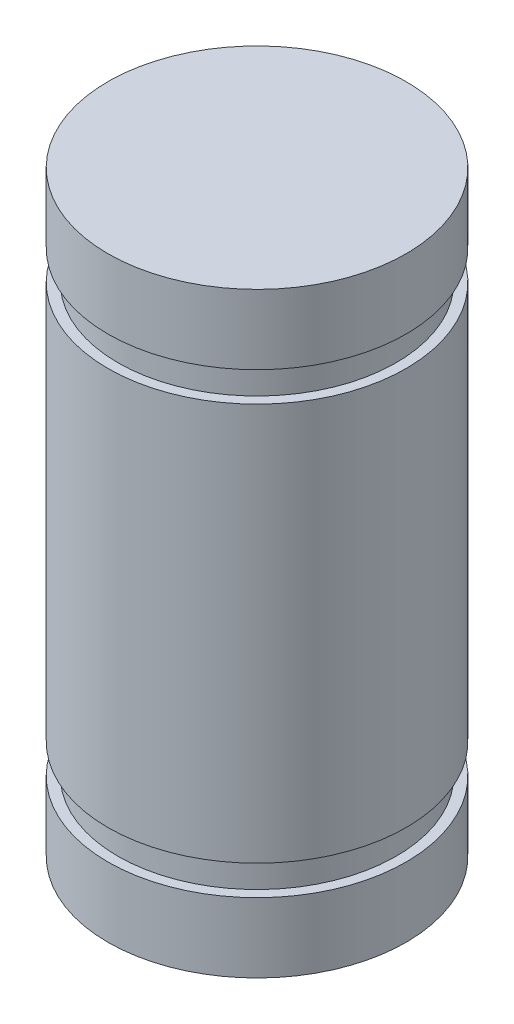
SolidWorks part; units mm, degrees
ref_plane "前视基准面" through (0, 0, 0) normal (0, 0, 1) x (1, 0, 0)
ref_plane "上视基准面" through (0, 0, 0) normal (0, 1, 0) x (1, 0, 0)
ref_plane "右视基准面" through (0, 0, 0) normal (1, 0, 0) x (0, 0, -1)
sketch "草图1" plane through (0, 0, 0) normal (0, 0, 1) x (1, 0, 0)
  line L0 (0, -6) -> (3, -6)
  line L1 (3, -6) -> (3, -4.6)
  line L2 (3, -4.6) -> (2.8, -4.6)
  line L3 (2.8, -4.6) -> (2.8, -4)
  line L4 (2.8, -4) -> (3, -4)
  line L5 (3, -4) -> (3, 4)
  line L6 (3, 4) -> (2.8, 4)
  line L7 (2.8, 4.6) -> (3, 4.6)
  line L8 (2.8, 4) -> (2.8, 4.6)
  line L9 (3, 4.6) -> (3, 6)
  line L10 (3, 6) -> (0, 6)
  line L11 (0, 6) -> (0, -6)
  dimension "D1" = 3
  dimension "D2" = 0.2
  dimension "D3" = 12
  dimension "D4" = 0.6
  dimension "D5" = 1.4
revolve "旋转1" add sketch "草图1" angle 360 about L11
